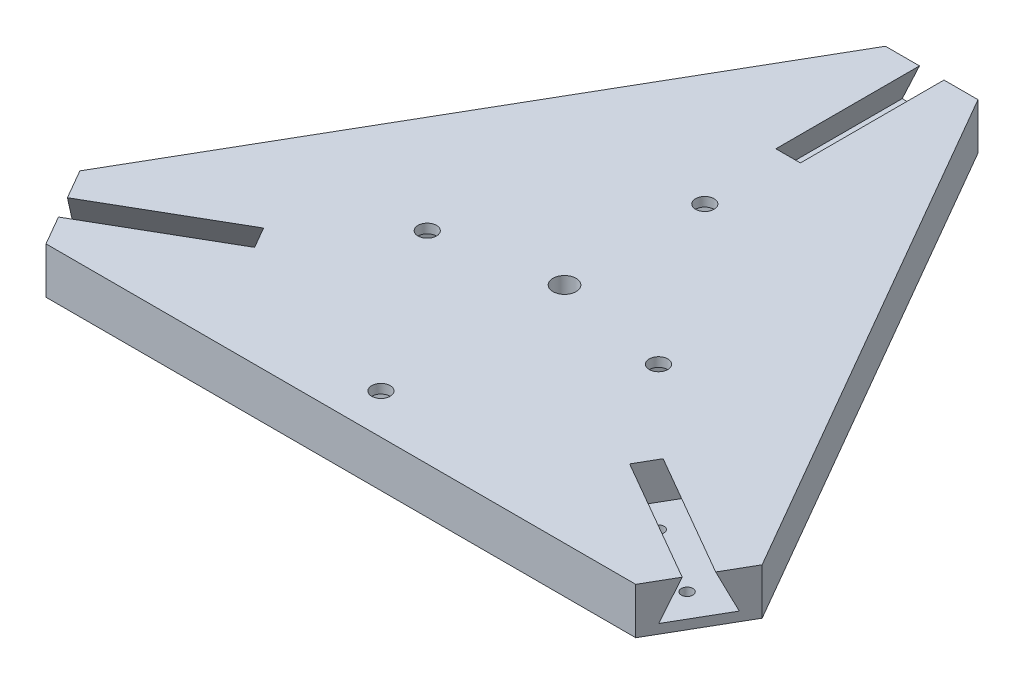
SolidWorks part; units mm, degrees
material "PLA"
ref_plane "Plan de face" through (0, 0, 0) normal (0, 0, 1) x (1, 0, 0)
ref_plane "Plan de dessus" through (0, 0, 0) normal (0, 1, 0) x (1, 0, 0)
ref_plane "Plan de droite" through (0, 0, 0) normal (1, 0, 0) x (0, 0, -1)
sketch "Esquisse1" plane through (0, 0, 0) normal (0, 1, 0) x (1, 0, 0)
  line L29 (-10, 79.3725) -> (10, 79.3725)
  line L30 (73.7386, -31.026) -> (63.7386, -48.3465)
  line L31 (-63.7386, -48.3465) -> (-73.7386, -31.026)
  line L32 (-10, 79.3725) -> (-73.7386, -31.026)
  line L33 (-63.7386, -48.3465) -> (63.7386, -48.3465)
  line L34 (73.7386, -31.026) -> (10, 79.3725)
  circle A7 centre (0, 0) radius 2.5
  circle A8 centre (0, 0) radius 79.3725 construction
  point P17 (0, 0)
  dimension "D1" = 20
  dimension "D4" = 20
  dimension "D5" = 80
  dimension "D6" = 80
  dimension "D3" = 80
  dimension "D9" = 5
  dimension "D12" = 79.3725
  dimension "D2" = 20
  dimension "D7" = 60
  dimension "D8" = 60
  dimension "D10" = 80
  dimension "D11" = 80
extrude "Boss.-Extru.1" add sketch "Esquisse1" along normal mid plane 10
sketch "Esquisse2" plane through (0, 5, 0) normal (0, 1, 0) x (1, 0, 0)
  line L0 (-68.7386, -39.6863) -> (0, 0) construction
  line L1 (-73.7386, -31.026) -> (-63.7386, -48.3465) construction
  circle A0 centre (-62.6851, -36.1913) radius 1.25
  circle A1 centre (-47.9107, -27.6613) radius 1.25
  dimension "D1" = 2.5
  dimension "D4" = 2.5
  dimension "D2" = 6.99
  dimension "D3" = 17.06
extrude "Enlèv. mat.-Extru.1" cut sketch "Esquisse2" against normal through all
pattern_circular "Répétition circulaire1" count 3 over 360 about axis through (0, 0, 0) along (0, 1, 0) of "Enlèv. mat.-Extru.1"
sketch "Esquisse4" plane through (0, -5, 0) normal (0, -1, 0) x (1, 0, 0)
  line L0 (0, 0) -> (25, 0) construction
  line L1 (25, 0) -> (25, 4.68) construction
  line L2 (0, 0) -> (-25, 0) construction
  line L3 (-25, 0) -> (-25, 4.68) construction
  circle A3 centre (0, -30.32) radius 2
  circle A7 centre (0, 39.68) radius 2
  circle A8 centre (25, 4.68) radius 2
  circle A9 centre (-25, 4.68) radius 2
  point P7 (0, 0)
  point P15 (0, 0)
  dimension "D3" = 25
  dimension "D4" = 4.68
  dimension "D7" = 4
  dimension "D8" = 39.68
  dimension "D11" = 70
  dimension "D2" = 4
  dimension "D5" = 25
  dimension "D9" = 4
  dimension "D10" = 4
  dimension "D6" = 4.68
extrude "Enlèv. mat.-Extru.3" cut sketch "Esquisse4" against normal through all
sketch "Esquisse5" plane through (0, -5, 0) normal (0, -1, 0) x (1, 0, 0)
  line L0 (-19.85, 34.53) -> (19.85, 34.53)
  line L1 (-19.85, 34.53) -> (-19.85, -25.17)
  line L2 (-19.85, -25.17) -> (19.85, -25.17)
  line L3 (19.85, -25.17) -> (19.85, 34.53)
  line L4 (-30.15, 44.83) -> (30.15, 44.83)
  line L5 (30.15, -35.47) -> (30.15, 44.83)
  line L6 (-30.15, -35.47) -> (30.15, -35.47)
  line L7 (-30.15, 44.83) -> (-30.15, -35.47)
  circle A0 centre (25, 4.68) radius 2 construction
  circle A1 centre (-25, 4.68) radius 2 construction
  circle A2 centre (0, 39.68) radius 2 construction
  circle A3 centre (0, -30.32) radius 2 construction
  dimension "D1" = 5.15
  dimension "D2" = 5.15
  dimension "D3" = 5.15
  dimension "D4" = 5.15
  dimension "D5" = 10.3
extrude "Enlèv. mat.-Extru.4" cut sketch "Esquisse5" against normal blind 8
sketch "Esquisse6" plane through (0, -5, 0) normal (0, -1, 0) x (1, 0, 0)
  line L4 (19.85, 34.53) -> (-19.85, 34.53) construction
  circle A0 centre (0, 20.18) radius 3.325
  circle A1 centre (0, 20.18) radius 6.325
  dimension "D2" = 6.65
  dimension "D3" = 3
  dimension "D1" = 14.35
extrude "Boss.-Extru.2" add sketch "Esquisse6" along normal blind 10
sketch "Esquisse7" plane through (-68.7386, 0, 39.6863) normal (-0.866, 0, 0.5) x (0.5, 0, 0.866)
  line L0 (-2.65, 5) -> (-6.38, -3)
  line L1 (-10, 5) -> (10, 5) construction
  line L2 (-6.38, -3) -> (6.38, -3)
  line L3 (6.38, -3) -> (2.65, 5)
  line L7 (-10, 5) -> (10, 5) construction
  line L8 (10, 5) -> (10, -5) construction
  line L9 (10, 5) -> (73.7386, 5) construction
  line L10 (-2.65, 5) -> (2.65, 5)
  point P0 (0, -3)
  point P13 (-2.2252, 5)
  point P16 (0, 5)
  dimension "D1" = 5.3
  dimension "D2" = 12.76
  dimension "D3" = 8
extrude "Enlèv. mat.-Extru.5" cut sketch "Esquisse7" against normal blind 31.04
pattern_circular "Répétition circulaire2" count 3 over 360 about axis through (0, 0, 0) along (0, 1, 0) of "Enlèv. mat.-Extru.5"
